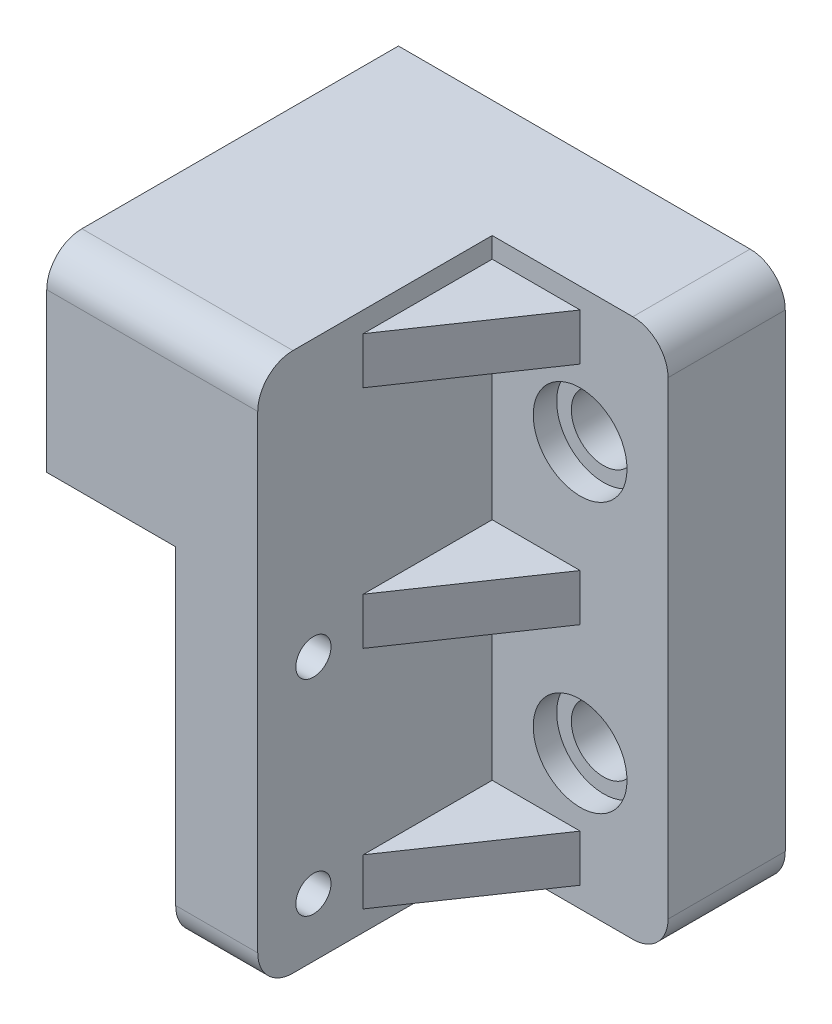
SolidWorks part; units mm, degrees
ref_plane "Plano frontal" through (0, 0, 0) normal (0, 0, 1) x (1, 0, 0)
ref_plane "Plano superior" through (0, 0, 0) normal (0, 1, 0) x (1, 0, 0)
ref_plane "Plano direito" through (0, 0, 0) normal (1, 0, 0) x (0, 0, -1)
sketch "Esboço1" plane through (0, 0, 0) normal (0, 1, 0) x (1, 0, 0)
  line L1 (-3.5, 15) -> (3.5, 15)
  line L2 (-3.5, 15) -> (-3.5, -15)
  line L3 (-3.5, -15) -> (3.5, -15)
  line L4 (3.5, 15) -> (3.5, -15)
  line L5 (-3.5, 15) -> (3.5, -15) construction
  line L6 (-3.5, -15) -> (3.5, 15) construction
  point P0 (0, 0)
  dimension "D1" = 7
  dimension "D2" = 30
extrude "Ressalto-extrusão1" add sketch "Esboço1" along normal blind 46
sketch "Esboço2" plane through (-3.5, 0, 0) normal (-1, 0, 0) x (0, 0, 1)
  line L0 (15, 46) -> (7.5, 46) construction
  line L1 (-15, 46) -> (15, 46) construction
  line L2 (7.5, 46) -> (7.5, 29.5) construction
  line L3 (-15, 46) -> (-7.5, 46) construction
  line L4 (-7.5, 46) -> (-7.5, 29.5) construction
  line L5 (0, 46) -> (0, 40) construction
  line L6 (0, 40) -> (-7.5, 40)
  line L7 (-7.5, 40) -> (-7.5, 29.5)
  line L8 (-7.5, 29.5) -> (-15, 29.5)
  line L9 (-15, 46) -> (-15, 0) construction
  line L10 (-15, 29.5) -> (-15, 46)
  line L11 (-15, 46) -> (15, 46)
  line L12 (15, 46) -> (15, 29.5)
  line L13 (15, 46) -> (15, 0) construction
  line L14 (15, 29.5) -> (7.5, 29.5)
  line L15 (7.5, 29.5) -> (7.5, 40)
  line L16 (7.5, 40) -> (0, 40)
  dimension "D1" = 7.5
  dimension "D2" = 7.5
  dimension "D3" = 16.5
  dimension "D4" = 16.5
  dimension "D5" = 6
extrude "Ressalto-extrusão2" add sketch "Esboço2" along normal blind 11
fillet "Filete1" radius 3 2 edges at (-14.5, 34.75, 7.5) (-14.5, 34.75, -7.5)
sketch "Esboço3" plane through (-3.5, 0, 0) normal (-1, 0, 0) x (0, 0, 1)
  line L0 (15, 0) -> (15, 27.5) construction
  line L2 (15, 29.5) -> (15, 0) construction
  line L3 (-15, 0) -> (-15, 27.5) construction
  line L4 (-15, 29.5) -> (-15, 0) construction
  line L5 (-15, 27.5) -> (15, 0) construction
  line L6 (15, 27.5) -> (-15, 0) construction
  line L7 (0, 13.75) -> (10.25, 13.75) construction
  line L8 (0, 13.75) -> (-10.25, 13.75) construction
  line L9 (10.25, 13.75) -> (10.25, 22.5) construction
  line L10 (-10.25, 13.75) -> (-10.25, 22.5) construction
  line L11 (-10.25, 13.75) -> (-10.25, 5) construction
  line L12 (10.25, 13.75) -> (10.25, 5) construction
  circle A0 centre (-10.25, 5) radius 1.5
  circle A1 centre (10.25, 5) radius 1.5
  circle A2 centre (-10.25, 22.5) radius 1.5
  circle A3 centre (10.25, 22.5) radius 1.5
  dimension "D9" = 3
  dimension "D10" = 3
  dimension "D11" = 3
  dimension "D12" = 3
  dimension "D1" = 27.5
  dimension "D2" = 27.5
  dimension "D3" = 10.25
  dimension "D4" = 10.25
  dimension "D5" = 8.75
  dimension "D6" = 8.75
  dimension "D7" = 8.75
  dimension "D8" = 8.75
extrude "Corte-extrusão1" cut sketch "Esboço3" against normal through all
sketch "Esboço4" plane through (3.5, 0, 0) normal (1, 0, 0) x (0, 0, -1)
  line L0 (-15, 46) -> (15, 46) construction
  line L1 (15, 0) -> (5, 0)
  line L2 (15, 0) -> (15, 46)
  line L3 (15, 46) -> (5, 46)
  line L4 (5, 0) -> (5, 46)
  dimension "D1" = 10
extrude "Ressalto-extrusão4" add sketch "Esboço4" along normal blind 15
sketch "Esboço5" plane through (0, 0, -5) normal (0, 0, 1) x (1, 0, 0)
  line L0 (11, 46) -> (18.5, 23) construction
  line L1 (18.5, 46) -> (3.5, 46) construction
  line L2 (18.5, 46) -> (18.5, 0) construction
  line L3 (18.5, 23) -> (11, 23) construction
  line L4 (11, 23) -> (11, 46) construction
  line L5 (11, 23) -> (11, 0) construction
  line L6 (18.5, 0) -> (3.5, 0) construction
  circle A0 centre (11, 11.5) radius 2.75
  circle A1 centre (11, 34.5) radius 2.75
  dimension "D1" = 5.5
  dimension "D2" = 5.5
extrude "Corte-extrusão2" cut sketch "Esboço5" against normal through all
sketch "Esboço6" plane through (0, 0, -5) normal (0, 0, 1) x (1, 0, 0)
  circle A0 centre (11, 11.5) radius 4
  circle A1 centre (11, 34.5) radius 4
  dimension "D1" = 8
  dimension "D2" = 8
extrude "Corte-extrusão3" cut sketch "Esboço6" against normal blind 2
sketch "Esboço7" plane through (0, 0, -5) normal (0, 0, 1) x (1, 0, 0)
  line L0 (11, 30.5) -> (11, 15.5) construction
  line L1 (11, 7.5) -> (11, 0) construction
  line L2 (18.5, 0) -> (3.5, 0) construction
  line L3 (11, 38.5) -> (11, 46) construction
  line L4 (18.5, 46) -> (3.5, 46) construction
  line L5 (11, 42.25) -> (3.5, 42.25) construction
  line L6 (3.5, 46) -> (3.5, 0) construction
  line L7 (11, 23) -> (3.5, 23) construction
  line L8 (11, 3.75) -> (3.5, 3.75) construction
  line L9 (3.5, 46) -> (3.5, 0) construction
  line L11 (3.5, 5.75) -> (11, 5.75)
  line L12 (3.5, 5.75) -> (3.5, 1.75)
  line L13 (3.5, 1.75) -> (11, 1.75)
  line L14 (11, 5.75) -> (11, 1.75)
  line L15 (3.5, 5.75) -> (11, 1.75) construction
  line L16 (3.5, 1.75) -> (11, 5.75) construction
  line L17 (3.5, 25) -> (11, 25)
  line L18 (3.5, 25) -> (3.5, 21)
  line L19 (3.5, 21) -> (11, 21)
  line L20 (11, 25) -> (11, 21)
  line L21 (3.5, 25) -> (11, 21) construction
  line L22 (3.5, 21) -> (11, 25) construction
  line L23 (3.5, 44.25) -> (11, 44.25)
  line L24 (3.5, 44.25) -> (3.5, 40.25)
  line L25 (3.5, 40.25) -> (11, 40.25)
  line L26 (11, 44.25) -> (11, 40.25)
  line L27 (3.5, 44.25) -> (11, 40.25) construction
  line L28 (3.5, 40.25) -> (11, 44.25) construction
  circle A0 centre (11, 34.5) radius 4 construction
  circle A1 centre (11, 34.5) radius 4 construction
  circle A2 centre (11, 11.5) radius 4 construction
  circle A3 centre (11, 11.5) radius 4 construction
  point P29 (7.25, 3.75)
  point P34 (7.25, 23)
  point P39 (7.25, 42.25)
  dimension "D1" = 4
  dimension "D2" = 4
  dimension "D3" = 4
extrude "Ressalto-extrusão5" add sketch "Esboço7" along normal blind 11
sketch "Esboço8" plane through (0, 1.75, 0) normal (0, -1, 0) x (1, 0, 0)
  line L0 (11, -5) -> (3.5, 6)
  line L1 (3.5, 6) -> (11, 6)
  line L2 (11, 6) -> (11, -5)
extrude "Corte-extrusão4" cut sketch "Esboço8" against normal through all
fillet "Filete2" radius 3 2 edges at (0, 0, 15) (-5.5, 46, 15)
fillet "Filete3" radius 3 2 edges at (18.5, 0, -10) (18.5, 46, -10)
sketch "Esboço9" plane through (0, 0, -15) normal (0, 0, -1) x (-1, 0, 0)
  line L0 (14.5, 46) -> (14.5, 40) construction
  line L1 (14.5, 46) -> (14.5, 29.5) construction
  line L2 (14.5, 43) -> (11.5, 43) construction
  circle A0 centre (11.5, 43) radius 2
  dimension "D3" = 4
  dimension "D1" = 6
  dimension "D2" = 3
extrude "Corte-extrusão5" cut sketch "Esboço9" against normal blind 22
ref_plane "Plano1" through (-14.75, 0, -14.75) normal (-0.7071, 0, -0.7071) x (0, -1, 0)
sketch "Esboço15" plane through (-14.75, 0, -14.75) normal (-0.7071, 0, -0.7071) x (0, -1, 0)
  line L0 (-46, -6.0104) -> (-38, -6.0104) construction
  circle A0 centre (-38, -6.0104) radius 1.5
  dimension "D2" = 3
  dimension "D1" = 8
extrude "Corte-extrusão6" cut sketch "Esboço15" against normal blind 22
sketch "Esboço16" plane through (0, 0, -15) normal (0, 0, -1) x (-1, 0, 0)
  line L0 (6.5, 39.5) -> (9.5, 43)
  line L1 (8.6213, 38) -> (11.5, 41)
  line L2 (6.5, 39.5) -> (8.6213, 38)
  line L3 (9.5, 43) -> (11.5, 41)
  circle A0 centre (11.5, 43) radius 2 construction
  ellipse E0 centre (6.5, 38) end of major axis (4.3787, 38) minor radius 1.5 construction
extrude "Corte-extrusão7" cut sketch "Esboço16" against normal blind 2.5
